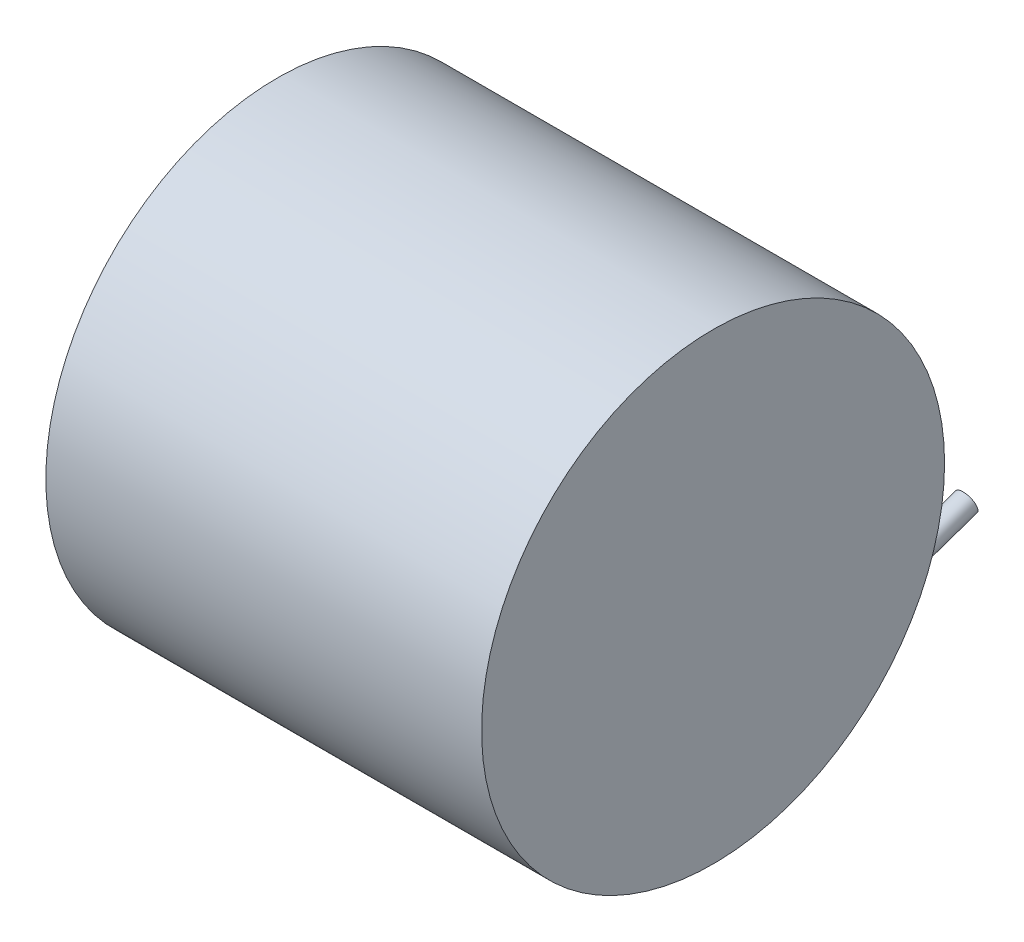
SolidWorks part; units mm, degrees
ref_plane "Front Plane" through (0, 0, 0) normal (0, 0, 1) x (1, 0, 0)
ref_plane "Top Plane" through (0, 0, 0) normal (0, 1, 0) x (1, 0, 0)
ref_plane "Right Plane" through (0, 0, 0) normal (1, 0, 0) x (0, 0, -1)
sketch "Sketch1" plane through (0, 0, 0) normal (1, 0, 0) x (0, 0, -1)
  circle A0 centre (0, 0) radius 42.5
  dimension "D1" = 85
extrude "Boss-Extrude1" add sketch "Sketch1" along normal mid plane 80
sketch "Sketch2" plane through (-40, 0, 0) normal (-1, 0, 0) x (0, 0, 1)
  circle A0 centre (-15.2907, 5.2889) radius 2
extrude "Boss-Extrude2" add sketch "Sketch2" along normal blind 15
sketch "Sketch3" plane through (0, 15.5273, -44.8905) normal (0, 0.3269, -0.9451) x (-1, 0, 0)
  circle A0 centre (-30, -35.6195) radius 2
extrude "Boss-Extrude3" add sketch "Sketch3" against normal blind 30
